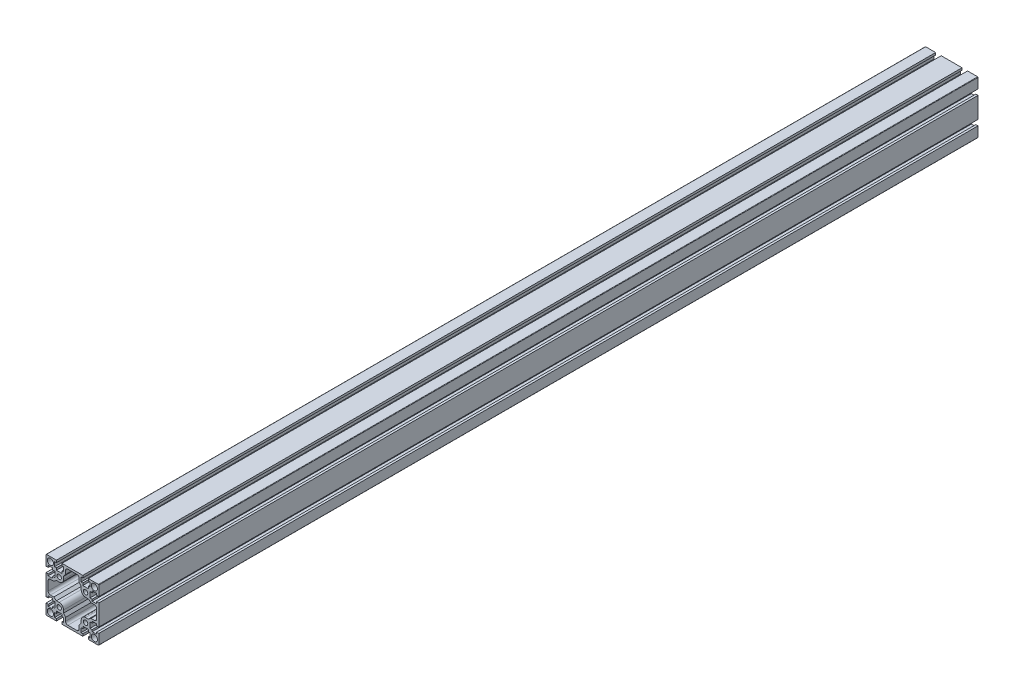
SolidWorks part; units mm, degrees
material "6063 T5"
ref_plane "Спереди" through (0, 0, 0) normal (0, 0, 1) x (1, 0, 0)
ref_plane "Сверху" through (0, 0, 0) normal (0, 1, 0) x (1, 0, 0)
ref_plane "Справа" through (0, 0, 0) normal (1, 0, 0) x (0, 0, -1)
sketch "Эскиз1" plane through (0, 0, 0) normal (0, 0, 1) x (1, 0, 0)
  line L0 (0, 30) -> (0, -30) construction
  line L1 (-30, 0) -> (30, 0) construction
  line L2 (-30, 20.15) -> (-30, 29.5)
  line L3 (-29.5, 30) -> (-20.15, 30)
  line L4 (0, 27.6) -> (-5.15, 27.6)
  line L5 (-7.75, 25) -> (-7.75, 21.1)
  line L6 (-7.75, 21.1) -> (-10, 18.1)
  line L7 (-10, 18.1) -> (-10, 15)
  line L8 (-15, 10) -> (-18.1, 10)
  line L9 (-18.1, 10) -> (-21.1, 7.75)
  line L10 (-21.1, 7.75) -> (-25, 7.75)
  line L11 (-27.6, 5.15) -> (-27.6, 0)
  line L12 (-9.85, 30) -> (0, 30)
  line L13 (-30, 9.85) -> (-30, 0)
  line L14 (-30.1393, 30.5564) -> (29.8607, 30.5564) construction
  line L15 (20.15, 30) -> (29.5, 30)
  line L16 (30, 29.5) -> (30, 20.15)
  line L17 (27.6, 0) -> (27.6, 5.15)
  line L18 (25, 7.75) -> (21.1, 7.75)
  line L19 (21.1, 7.75) -> (18.1, 10)
  line L20 (18.1, 10) -> (15, 10)
  line L21 (10, 15) -> (10, 18.1)
  line L22 (10, 18.1) -> (7.75, 21.1)
  line L23 (7.75, 21.1) -> (7.75, 25)
  line L24 (5.15, 27.6) -> (0, 27.6)
  line L25 (30, 9.85) -> (30, 0)
  line L26 (9.85, 30) -> (0, 30)
  line L27 (30, -20.15) -> (30, -29.5)
  line L28 (29.5, -30) -> (20.15, -30)
  line L29 (0, -27.6) -> (5.15, -27.6)
  line L30 (7.75, -25) -> (7.75, -21.1)
  line L31 (7.75, -21.1) -> (10, -18.1)
  line L32 (10, -18.1) -> (10, -15)
  line L33 (15, -10) -> (18.1, -10)
  line L34 (18.1, -10) -> (21.1, -7.75)
  line L35 (21.1, -7.75) -> (25, -7.75)
  line L36 (27.6, -5.15) -> (27.6, 0)
  line L37 (9.85, -30) -> (0, -30)
  line L38 (30, -9.85) -> (30, 0)
  line L39 (-20.15, -30) -> (-29.5, -30)
  line L40 (-30, -29.5) -> (-30, -20.15)
  line L41 (-27.6, 0) -> (-27.6, -5.15)
  line L42 (-25, -7.75) -> (-21.1, -7.75)
  line L43 (-21.1, -7.75) -> (-18.1, -10)
  line L44 (-18.1, -10) -> (-15, -10)
  line L45 (-10, -15) -> (-10, -18.1)
  line L46 (-10, -18.1) -> (-7.75, -21.1)
  line L47 (-7.75, -21.1) -> (-7.75, -25)
  line L48 (-5.15, -27.6) -> (0, -27.6)
  line L49 (-30, -9.85) -> (-30, 0)
  line L50 (-9.85, -30) -> (0, -30)
  circle A1 centre (-25, 25) radius 3.5
  circle A2 centre (-15, 15) radius 2.5
  arc A3 (-30, 29.5) -> (-29.5, 30) centre (-29.5, 29.5) cw
  arc A4 (-5.15, 27.6) -> (-7.75, 25) centre (-5.15, 25) ccw
  arc A5 (-10, 15) -> (-15, 10) centre (-15, 15) cw
  arc A6 (-25, 7.75) -> (-27.6, 5.15) centre (-25, 5.15) ccw
  circle A7 centre (25, 25) radius 3.5
  circle A8 centre (15, 15) radius 2.5
  arc A9 (29.5, 30) -> (30, 29.5) centre (29.5, 29.5) cw
  arc A10 (27.6, 5.15) -> (25, 7.75) centre (25, 5.15) ccw
  arc A11 (15, 10) -> (10, 15) centre (15, 15) cw
  arc A12 (7.75, 25) -> (5.15, 27.6) centre (5.15, 25) ccw
  circle A13 centre (25, -25) radius 3.5
  circle A14 centre (15, -15) radius 2.5
  arc A15 (30, -29.5) -> (29.5, -30) centre (29.5, -29.5) cw
  arc A16 (5.15, -27.6) -> (7.75, -25) centre (5.15, -25) ccw
  arc A17 (10, -15) -> (15, -10) centre (15, -15) cw
  arc A18 (25, -7.75) -> (27.6, -5.15) centre (25, -5.15) ccw
  circle A19 centre (-25, -25) radius 3.5
  circle A20 centre (-15, -15) radius 2.5
  arc A21 (-29.5, -30) -> (-30, -29.5) centre (-29.5, -29.5) cw
  arc A22 (-27.6, -5.15) -> (-25, -7.75) centre (-25, -5.15) ccw
  arc A23 (-15, -10) -> (-10, -15) centre (-15, -15) cw
  arc A24 (-7.75, -25) -> (-5.15, -27.6) centre (-5.15, -25) ccw
  point P10 (-15, 20)
  point P11 (-15, 30)
  point P16 (-20, 15)
  point P123 (0, 0)
  line B0 (-20.15, 30) -> (-18.15, 30)
  line B1 (-18.15, 30) -> (-18.15, 27.5)
  line B2 (-18.15, 27.5) -> (-20.15, 27.5)
  line B3 (-20.15, 27.5) -> (-20.15, 22.5)
  line B4 (-20.15, 22.5) -> (-18.15, 22.5)
  line B5 (-18.15, 22.5) -> (-18.15, 20)
  line B6 (-18.15, 20) -> (-11.85, 20)
  line B7 (-11.85, 20) -> (-11.85, 22.5)
  line B8 (-11.85, 22.5) -> (-9.85, 22.5)
  line B9 (-9.85, 22.5) -> (-9.85, 27.5)
  line B10 (-9.85, 27.5) -> (-11.85, 27.5)
  line B11 (-11.85, 27.5) -> (-11.85, 30)
  line B12 (-11.85, 30) -> (-9.85, 30)
  line B13 (-9.85, 30) -> (-20.15, 30) construction
  line B14 (-30, 9.85) -> (-30, 11.85)
  line B15 (-30, 11.85) -> (-27.5, 11.85)
  line B16 (-27.5, 11.85) -> (-27.5, 9.85)
  line B17 (-27.5, 9.85) -> (-22.5, 9.85)
  line B18 (-22.5, 9.85) -> (-22.5, 11.85)
  line B19 (-22.5, 11.85) -> (-20, 11.85)
  line B20 (-20, 11.85) -> (-20, 18.15)
  line B21 (-20, 18.15) -> (-22.5, 18.15)
  line B22 (-22.5, 18.15) -> (-22.5, 20.15)
  line B23 (-22.5, 20.15) -> (-27.5, 20.15)
  line B24 (-27.5, 20.15) -> (-27.5, 18.15)
  line B25 (-27.5, 18.15) -> (-30, 18.15)
  line B26 (-30, 18.15) -> (-30, 20.15)
  line B27 (-30, 20.15) -> (-30, 9.85) construction
  line B28 (30, 20.15) -> (30, 18.15)
  line B29 (30, 18.15) -> (27.5, 18.15)
  line B30 (27.5, 18.15) -> (27.5, 20.15)
  line B31 (27.5, 20.15) -> (22.5, 20.15)
  line B32 (22.5, 20.15) -> (22.5, 18.15)
  line B33 (22.5, 18.15) -> (20, 18.15)
  line B34 (20, 18.15) -> (20, 11.85)
  line B35 (20, 11.85) -> (22.5, 11.85)
  line B36 (22.5, 11.85) -> (22.5, 9.85)
  line B37 (22.5, 9.85) -> (27.5, 9.85)
  line B38 (27.5, 9.85) -> (27.5, 11.85)
  line B39 (27.5, 11.85) -> (30, 11.85)
  line B40 (30, 11.85) -> (30, 9.85)
  line B41 (30, 9.85) -> (30, 20.15) construction
  line B42 (9.85, 30) -> (11.85, 30)
  line B43 (11.85, 30) -> (11.85, 27.5)
  line B44 (11.85, 27.5) -> (9.85, 27.5)
  line B45 (9.85, 27.5) -> (9.85, 22.5)
  line B46 (9.85, 22.5) -> (11.85, 22.5)
  line B47 (11.85, 22.5) -> (11.85, 20)
  line B48 (11.85, 20) -> (18.15, 20)
  line B49 (18.15, 20) -> (18.15, 22.5)
  line B50 (18.15, 22.5) -> (20.15, 22.5)
  line B51 (20.15, 22.5) -> (20.15, 27.5)
  line B52 (20.15, 27.5) -> (18.15, 27.5)
  line B53 (18.15, 27.5) -> (18.15, 30)
  line B54 (18.15, 30) -> (20.15, 30)
  line B55 (20.15, 30) -> (9.85, 30) construction
  line B56 (20.15, -30) -> (18.15, -30)
  line B57 (18.15, -30) -> (18.15, -27.5)
  line B58 (18.15, -27.5) -> (20.15, -27.5)
  line B59 (20.15, -27.5) -> (20.15, -22.5)
  line B60 (20.15, -22.5) -> (18.15, -22.5)
  line B61 (18.15, -22.5) -> (18.15, -20)
  line B62 (18.15, -20) -> (11.85, -20)
  line B63 (11.85, -20) -> (11.85, -22.5)
  line B64 (11.85, -22.5) -> (9.85, -22.5)
  line B65 (9.85, -22.5) -> (9.85, -27.5)
  line B66 (9.85, -27.5) -> (11.85, -27.5)
  line B67 (11.85, -27.5) -> (11.85, -30)
  line B68 (11.85, -30) -> (9.85, -30)
  line B69 (9.85, -30) -> (20.15, -30) construction
  line B70 (30, -9.85) -> (30, -11.85)
  line B71 (30, -11.85) -> (27.5, -11.85)
  line B72 (27.5, -11.85) -> (27.5, -9.85)
  line B73 (27.5, -9.85) -> (22.5, -9.85)
  line B74 (22.5, -9.85) -> (22.5, -11.85)
  line B75 (22.5, -11.85) -> (20, -11.85)
  line B76 (20, -11.85) -> (20, -18.15)
  line B77 (20, -18.15) -> (22.5, -18.15)
  line B78 (22.5, -18.15) -> (22.5, -20.15)
  line B79 (22.5, -20.15) -> (27.5, -20.15)
  line B80 (27.5, -20.15) -> (27.5, -18.15)
  line B81 (27.5, -18.15) -> (30, -18.15)
  line B82 (30, -18.15) -> (30, -20.15)
  line B83 (30, -20.15) -> (30, -9.85) construction
  line B84 (-30, -20.15) -> (-30, -18.15)
  line B85 (-30, -18.15) -> (-27.5, -18.15)
  line B86 (-27.5, -18.15) -> (-27.5, -20.15)
  line B87 (-27.5, -20.15) -> (-22.5, -20.15)
  line B88 (-22.5, -20.15) -> (-22.5, -18.15)
  line B89 (-22.5, -18.15) -> (-20, -18.15)
  line B90 (-20, -18.15) -> (-20, -11.85)
  line B91 (-20, -11.85) -> (-22.5, -11.85)
  line B92 (-22.5, -11.85) -> (-22.5, -9.85)
  line B93 (-22.5, -9.85) -> (-27.5, -9.85)
  line B94 (-27.5, -9.85) -> (-27.5, -11.85)
  line B95 (-27.5, -11.85) -> (-30, -11.85)
  line B96 (-30, -11.85) -> (-30, -9.85)
  line B97 (-30, -9.85) -> (-30, -20.15) construction
  line B98 (-9.85, -30) -> (-11.85, -30)
  line B99 (-11.85, -30) -> (-11.85, -27.5)
  line B100 (-11.85, -27.5) -> (-9.85, -27.5)
  line B101 (-9.85, -27.5) -> (-9.85, -22.5)
  line B102 (-9.85, -22.5) -> (-11.85, -22.5)
  line B103 (-11.85, -22.5) -> (-11.85, -20)
  line B104 (-11.85, -20) -> (-18.15, -20)
  line B105 (-18.15, -20) -> (-18.15, -22.5)
  line B106 (-18.15, -22.5) -> (-20.15, -22.5)
  line B107 (-20.15, -22.5) -> (-20.15, -27.5)
  line B108 (-20.15, -27.5) -> (-18.15, -27.5)
  line B109 (-18.15, -27.5) -> (-18.15, -30)
  line B110 (-18.15, -30) -> (-20.15, -30)
  line B111 (-20.15, -30) -> (-9.85, -30) construction
  dimension "D5" = 7
  dimension "D7" = 5
  dimension "D8" = 0.5
  dimension "D9" = 5
  dimension "D12" = 2.6
  dimension "D1" = 60
  dimension "D2" = 30
  dimension "D3" = 50
  dimension "D4" = 50
  dimension "D6" = 60
  dimension "D10" = 15.5
  dimension "D11" = 2.4
  dimension "D13" = 2.4
  dimension "D14" = 6.5
  dimension "D15" = 15.5
  dimension "D16" = 9.5
  dimension "D17" = 9.5
  dimension "D18" = 6.5
sketch_block_instance "Блок1-1"
sketch_block "Блок1" parameters "D1"=10.3, "D2"=6.3, "D3"=2.5, "D4"=7.5, "D5"=10
sketch_block_instance "Блок1-3"
sketch_block_instance "Блок1-4"
sketch_block_instance "Блок1-5"
sketch_block_instance "Блок1-6"
sketch_block_instance "Блок1-7"
sketch_block_instance "Блок1-8"
sketch_block_instance "Блок1-9"
extrude "Бобышка-Вытянуть1" add sketch "Эскиз1" along normal blind 1000 contours B110 B109 B108 B107 B106 B105 B104 B103 B102 B101 B100 B99 B98 L50 L37 B68 B67 B66 B65 B64 B63 B62 B61 B60 B59 B58 B57 B56 L28 A15 L27 B82 B81 B80 B79 B78 B77 B76 B75 B74 B73 B72 B71 B70 L38 L25 B40 B39 B38 B37 B36
